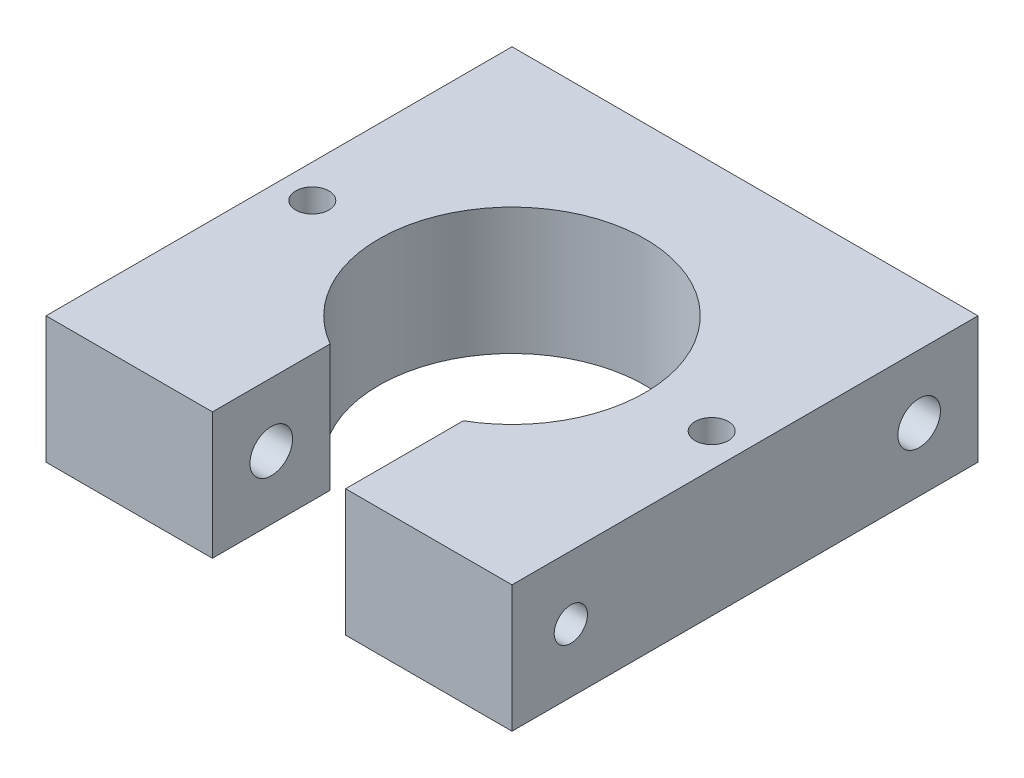
SolidWorks part; units mm, degrees
material "6061-T6 (SS)"
ref_plane "Front" through (0, 0, 0) normal (0, 0, 1) x (1, 0, 0)
ref_plane "Top" through (0, 0, 0) normal (0, 1, 0) x (1, 0, 0)
ref_plane "Right" through (0, 0, 0) normal (1, 0, 0) x (0, 0, -1)
sketch "Sketch1" plane through (0, 0, 0) normal (0, 1, 0) x (1, 0, 0)
  line L0 (-17.5, 0) -> (17.5, 0) construction
  line L1 (0, 17.5) -> (0, -17.5) construction
  line L2 (-17.5, 17.5) -> (-5, 17.5)
  line L3 (17.5, 17.5) -> (17.5, -17.5)
  line L4 (17.5, -17.5) -> (5, -17.5)
  line L5 (-17.5, -17.5) -> (-17.5, 17.5)
  line L6 (-5, 17.5) -> (5, 17.5)
  line L8 (5, 17.5) -> (17.5, 17.5)
  line L9 (5, -8.6603) -> (5, -17.5)
  line L10 (-5, -17.5) -> (-17.5, -17.5)
  line L11 (-5, -8.6603) -> (-5, -17.5)
  circle A0 centre (0, 0) radius 10 construction
  arc A1 (-5, -8.6603) -> (-5, 8.6603) centre (0, 0) cw
  arc A2 (5, 8.6603) -> (5, -8.6603) centre (0, 0) cw
  arc A3 (-5, 8.6603) -> (5, 8.6603) centre (0, 0) cw
  point P10 (-17.5, 15)
  point P11 (-5, 17.5)
  point P12 (5, 17.5)
  point P13 (0, 17.5)
  point P14 (-5, -17.5)
  point P15 (5, -17.5)
  point P18 (-5, 8.6603)
  point P19 (-5, -8.6603)
  point P25 (5, 8.6603)
  point P26 (5, -8.6603)
  point P30 (0, 10)
  point P32 (-13.75, -17.5)
  point P33 (-17.5, -11.6651)
  dimension "D1" = 12.5
  dimension "D4" = 5.8349
  dimension "D2" = 35
  dimension "D3" = 35
extrude "Boss-Extrude1" add sketch "Sketch1" along normal blind 9.525
hole_wizard "Tap Drill for M3x0.5 Tap1" positions "Sketch3" profile "Sketch2" hole size "M3x0.5" standard "ANSI Metric" end condition through all
sketch "Sketch3" plane through (0, 9.525, 0) normal (0, 1, 0) x (1, 0, 0)
  line L0 (-17.5, 17.5) -> (-17.5, -17.5) construction
  line L1 (-17.5, -17.5) -> (-5, -17.5) construction
  point P0 (-15, 0)
  dimension "D1" = 2.5
  dimension "D2" = 17.5
sketch "Sketch2" plane through (-15, 9.525, 0) normal (1, 0, 0) x (0, 0, 1)
  line L0 (0, 0) -> (0, 9.525)
  line L1 (0, 9.525) -> (1.25, 9.525)
  line L2 (1.25, 9.525) -> (1.25, 0)
  line L5 (1.25, 0) -> (0, 0)
  line L11 (0, -6.35) -> (0, 107.95) construction
  dimension "Thru Hole Dia." = 2.5
  dimension "Thru Hole Depth" = 9.525
hole_wizard "Tap Drill for M3x0.5 Tap2" positions "Sketch5" profile "Sketch4" hole size "M3x0.5" standard "ANSI Metric" end condition through all
sketch "Sketch5" plane through (0, 9.525, 0) normal (0, 1, 0) x (1, 0, 0)
  line L0 (17.5, -17.5) -> (17.5, 17.5) construction
  line L2 (5, -17.5) -> (17.5, -17.5) construction
  point P0 (15, 0)
  dimension "D1" = 2.5
  dimension "D2" = 17.5
sketch "Sketch4" plane through (15, 9.525, 0) normal (1, 0, 0) x (0, 0, 1)
  line L0 (0, 0) -> (0, 9.525)
  line L1 (0, 9.525) -> (1.25, 9.525)
  line L2 (1.25, 9.525) -> (1.25, 0)
  line L5 (1.25, 0) -> (0, 0)
  line L11 (0, -6.35) -> (0, 107.95) construction
  dimension "Thru Hole Dia." = 2.5
  dimension "Thru Hole Depth" = 9.525
hole_wizard "Tap Drill for M3x0.5 Tap3" positions "Sketch9" profile "Sketch8" hole size "M3x0.5" standard "ANSI Metric"
sketch "Sketch9" plane through (17.5, 0, 0) normal (1, 0, 0) x (0, 0, -1)
  line L0 (17.5, 9.525) -> (17.5, 0) construction
  line L1 (-17.5, 9.525) -> (17.5, 9.525) construction
  line L2 (-17.5, 9.525) -> (-17.5, 0) construction
  point P0 (13.0801, 4.7625)
  point P3 (17.5, 4.7625)
  point P9 (-13.0801, 4.7625)
  dimension "D1" = 4.4199
  dimension "D2" = 4.7625
  dimension "D3" = 4.4199
  dimension "D4" = 4.7625
sketch "Sketch8" plane through (17.5, 4.7625, -13.0801) normal (0, 1, 0) x (0, 0, -1)
  line L0 (0, 0) -> (0, 35)
  line L1 (0, 35) -> (1.25, 35)
  line L2 (1.25, 35) -> (1.25, 0)
  line L5 (1.25, 0) -> (0, 0)
  line L11 (0, -6.35) -> (0, 107.95) construction
  dimension "Thru Hole Dia." = 2.5
  dimension "Thru Hole Depth" = 35
hole_wizard "M3 Clearance Hole1" positions "Sketch11" profile "Sketch10" hole size "M3" standard "ANSI Metric"
sketch "Sketch11" plane through (-17.5, 0, 0) normal (-1, 0, 0) x (0, 0, 1)
  line L0 (-17.5, 9.525) -> (-17.5, 0) construction
  line L1 (-17.5, 9.525) -> (17.5, 9.525) construction
  line L2 (17.5, 9.525) -> (17.5, 0) construction
  point P0 (-13.0801, 4.7625)
  point P7 (13.0802, 4.7625)
  dimension "D1" = 4.4199
  dimension "D2" = 4.7625
  dimension "D3" = 4.4199
  dimension "D4" = 4.7625
sketch "Sketch10" plane through (-17.5, 4.7625, -13.0801) normal (0, 1, 0) x (0, 0, 1)
  line L0 (0, 0) -> (0, 35)
  line L1 (0, 35) -> (1.6, 35)
  line L2 (1.6, 35) -> (1.6, 0)
  line L5 (1.6, 0) -> (0, 0)
  line L11 (0, -6.35) -> (0, 107.95) construction
  dimension "Thru Hole Dia." = 3.2
  dimension "Thru Hole Depth" = 35
